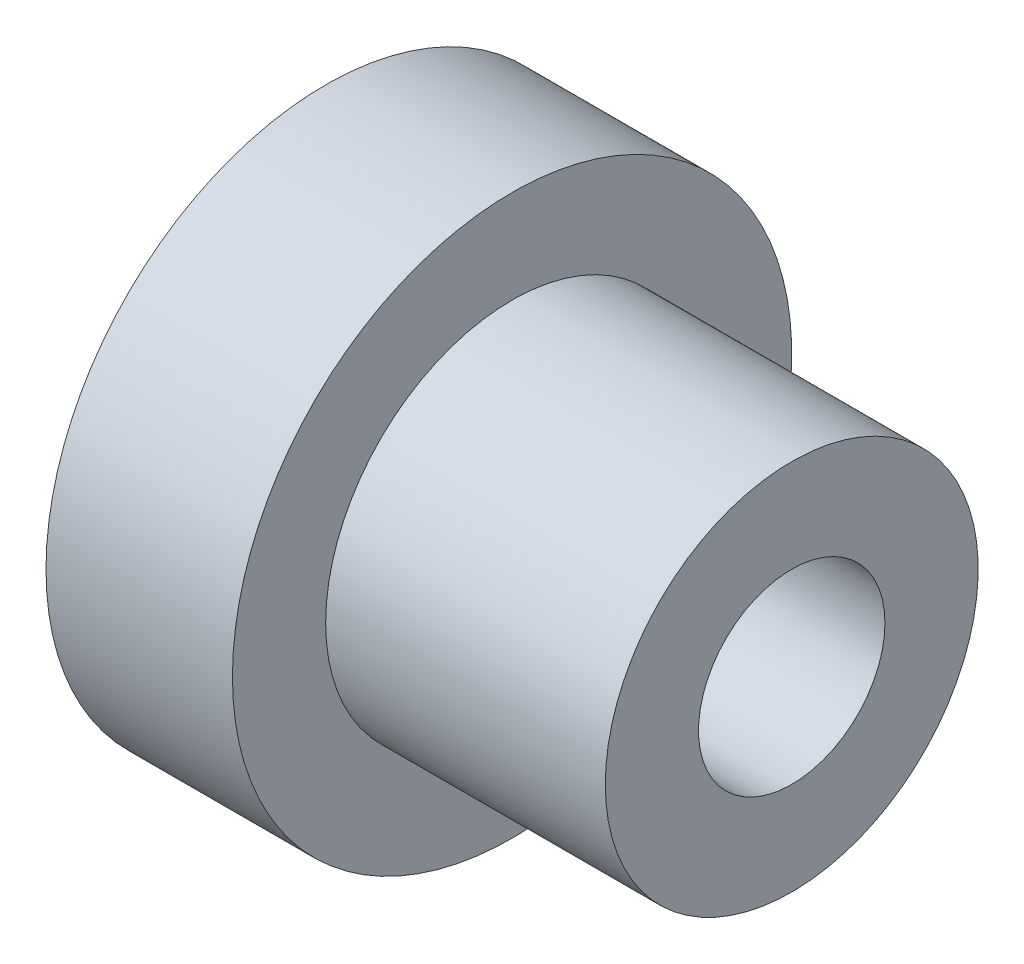
SolidWorks part; units mm, degrees
ref_plane "Plan de face" through (0, 0, 0) normal (0, 0, 1) x (1, 0, 0)
ref_plane "Plan de dessus" through (0, 0, 0) normal (0, 1, 0) x (1, 0, 0)
ref_plane "Plan de droite" through (0, 0, 0) normal (1, 0, 0) x (0, 0, -1)
sketch "Esquisse3" plane through (0, 0, 0) normal (0, 0, 1) x (1, 0, 0)
  line L0 (0, 0) -> (0, 4.5)
  line L1 (0, 4.5) -> (3, 4.5)
  line L2 (3, 4.5) -> (3, 3)
  line L3 (3, 3) -> (7.5, 3)
  line L4 (7.5, 3) -> (7.5, 0)
  line L5 (7.5, 0) -> (0, 0)
  line L6 (-5.5166, 0) -> (11.7258, 0) construction
  dimension "D1" = 3
  dimension "D2" = 4.5
  dimension "D3" = 4.5
  dimension "D4" = 3
revolve "Révolution1" add sketch "Esquisse3" angle 360 about L6
sketch "Esquisse4" plane through (7.5, 0, 0) normal (1, 0, 0) x (0, 0, -1)
  circle A0 centre (0, 0) radius 1.5
extrude "Enlèv. mat.-Extru.1" cut sketch "Esquisse4" against normal through all
